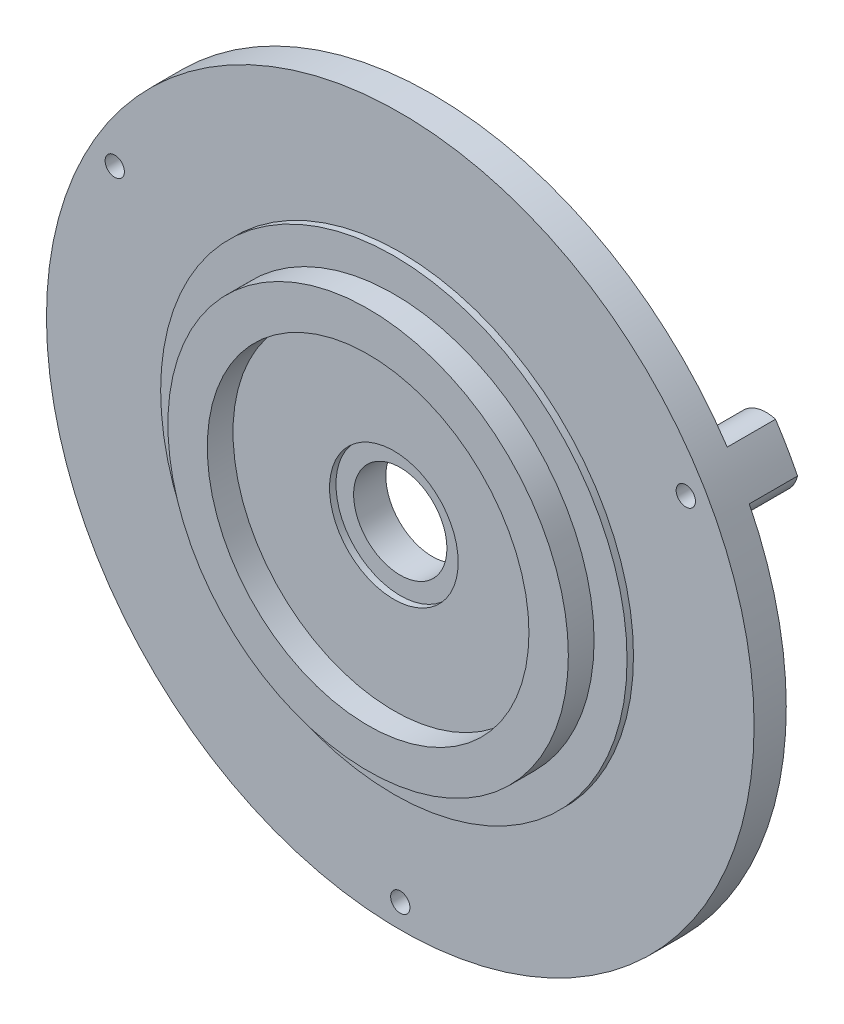
SolidWorks part; units mm, degrees
ref_plane "前视基准面" through (0, 0, 0) normal (0, 0, 1) x (1, 0, 0)
ref_plane "上视基准面" through (0, 0, 0) normal (0, 1, 0) x (1, 0, 0)
ref_plane "右视基准面" through (0, 0, 0) normal (1, 0, 0) x (0, 0, -1)
sketch "草图1" plane through (0, 0, 0) normal (0, 0, 1) x (1, 0, 0)
  circle A0 centre (0, 0) radius 22
extrude "凸台-拉伸1" add sketch "草图1" along normal blind 2
sketch "草图2" plane through (0, 0, 2) normal (0, 0, 1) x (1, 0, 0)
  circle A0 centre (0, 0) radius 12.45
  circle A1 centre (0, 0) radius 10
extrude "凸台-拉伸2" add sketch "草图2" along normal blind 2
sketch "草图3" plane through (0, 0, 2) normal (0, 0, 1) x (1, 0, 0)
  circle A0 centre (0, 0) radius 2.9
extrude "切除-拉伸1" cut sketch "草图3" against normal blind 11
sketch "草图4" plane through (0, 0, 0) normal (0, 0, -1) x (-1, 0, 0)
  line L0 (0, 0) -> (0, -20.5) construction
  arc A1 (1.3698, -21.9573) -> (-1.3698, -21.9573) centre (0, -20.5) ccw
  arc A2 (-19.7005, 9.7924) -> (-18.3307, 12.1649) centre (-17.7535, 10.25) ccw
  arc A3 (18.3307, 12.1649) -> (19.7005, 9.7924) centre (17.7535, 10.25) ccw
  arc A4 (-1.3698, -21.9573) -> (1.3698, -21.9573) centre (0, 0) ccw
  arc A5 (-18.3307, 12.1649) -> (-19.7005, 9.7924) centre (0, 0) ccw
  arc A6 (19.7005, 9.7924) -> (18.3307, 12.1649) centre (0, 0) ccw
  dimension "D1" = 3
  dimension "D2" = 20.5
extrude "凸台-拉伸3" add sketch "草图4" along normal blind 3
sketch "草图5" plane through (0, 0, -3) normal (0, 0, -1) x (-1, 0, 0)
  circle A1 centre (0, -20.5) radius 0.6
  circle A2 centre (-17.7535, 10.25) radius 0.6
  circle A3 centre (17.7535, 10.25) radius 0.6
extrude "切除-拉伸2" cut sketch "草图5" against normal blind 16
sketch "草图6" plane through (0, 0, 2) normal (0, 0, 1) x (1, 0, 0)
  circle A0 centre (0, 0) radius 14.5
  circle A3 centre (0, 0) radius 4
extrude "凸台-拉伸4" add sketch "草图6" along normal blind 0.4
